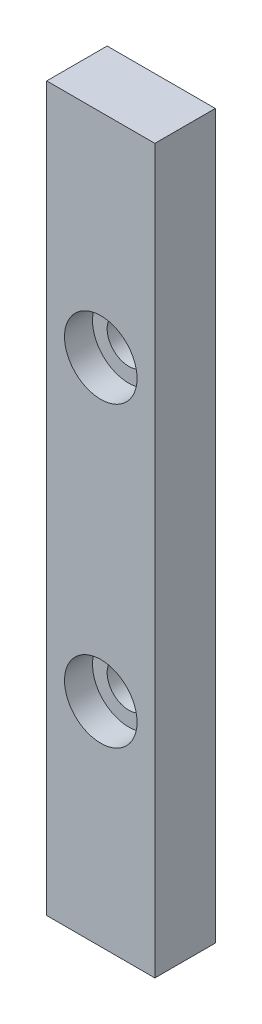
SolidWorks part; units mm, degrees
material "6061-T6 (SS)"
ref_plane "Front Plane" through (0, 0, 0) normal (0, 0, 1) x (1, 0, 0)
ref_plane "Top Plane" through (0, 0, 0) normal (0, 1, 0) x (1, 0, 0)
ref_plane "Right Plane" through (0, 0, 0) normal (1, 0, 0) x (0, 0, -1)
sketch "Sketch1" plane through (0, 0, 0) normal (0, 0, 1) x (1, 0, 0)
  line L1 (0, 0) -> (8.5, 0)
  line L2 (0, 0) -> (0, -56.8)
  line L3 (0, -56.8) -> (8.5, -56.8)
  line L4 (8.5, 0) -> (8.5, -56.8)
  dimension "D1" = 56.8
  dimension "D2" = 8.5
extrude "Boss-Extrude1" add sketch "Sketch1" along normal blind 4.75
sketch "Sketch3" plane through (0, 0, 4.75) normal (0, 0, 1) x (1, 0, 0)
  line L0 (8.5, 0) -> (0, 0) construction
  line L2 (0, -56.8) -> (8.5, -56.8) construction
  line L4 (8.5, -56.8) -> (8.5, 0) construction
  point P9 (4.25, -16.7)
  point P10 (4.25, -40.1)
  dimension "D1" = 16.7
  dimension "D2" = 16.7
  dimension "D3" = 4.25
  dimension "D4" = 4.25
hole_wizard "M3 Clearance Hole1" positions "Sketch4" profile "Sketch5" hole size "M3" standard "ANSI Metric"
sketch "Sketch4" plane through (0, 0, 4.75) normal (0, 0, 1) x (1, 0, 0)
  point P0 (4.25, -16.7)
  point P3 (4.25, -40.1)
sketch "Sketch5" plane through (4.25, -16.7, 4.75) normal (1, 0, 0) x (0, -1, 0)
  line L0 (0, 0) -> (0, 6.0215)
  line L1 (0, 6.0215) -> (1.7, 5)
  line L2 (1.7, 5) -> (1.7, 0)
  line L5 (1.7, 0) -> (0, 0)
  line L10 (0, 6.0215) -> (-1.7, 5) construction
  line L11 (0, -6.35) -> (0, 107.95) construction
  dimension "Hole Dia." = 3.4
  dimension "Hole Depth" = 5
  dimension "Drill Angle" = 118
sketch "Sketch6" plane through (0, 0, 4.75) normal (0, 0, 1) x (1, 0, 0)
  circle A0 centre (4.25, -16.7) radius 2.85
  circle A1 centre (4.25, -40.1) radius 2.85
  dimension "D1" = 5.7
extrude "Cut-Extrude1" cut sketch "Sketch6" against normal blind 2.2
